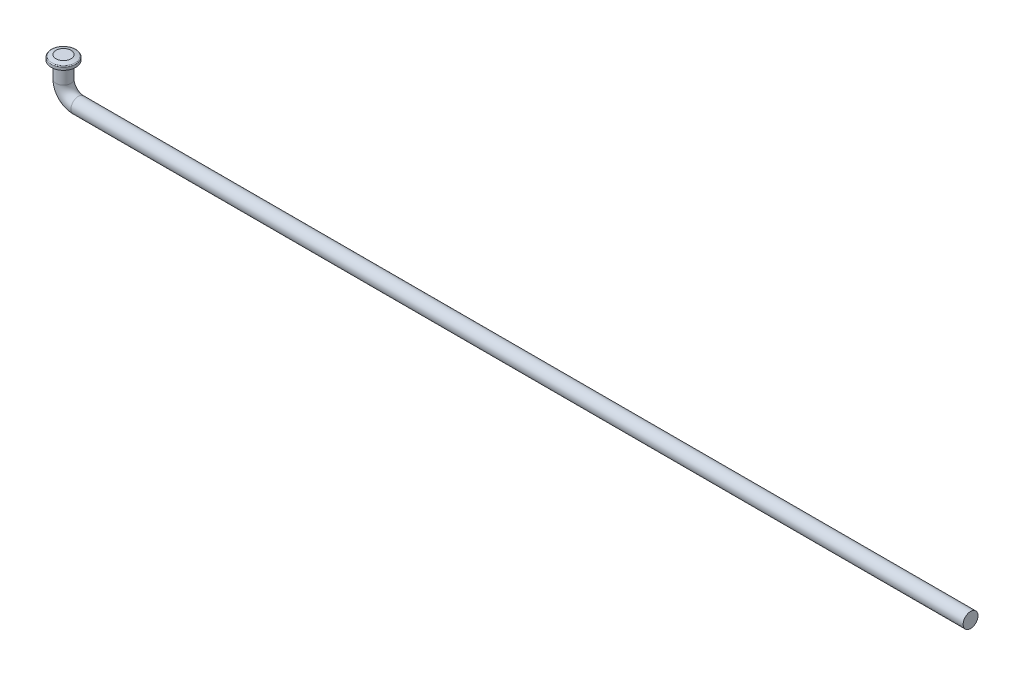
SolidWorks part; units mm, degrees
ref_plane "Спереди" through (0, 0, 0) normal (0, 0, 1) x (1, 0, 0)
ref_plane "Сверху" through (0, 0, 0) normal (0, 1, 0) x (1, 0, 0)
ref_plane "Справа" through (0, 0, 0) normal (1, 0, 0) x (0, 0, -1)
sketch "Эскиз1" plane through (0, 0, 0) normal (0, 0, 1) x (1, 0, 0)
  line L0 (-90, 0) -> (90, 0)
  line L1 (-93, 3) -> (-93, 6)
  arc A0 (-90, 0) -> (-93, 3) centre (-90, 3) cw
  point P4 (0, 0)
  dimension "D1" = 3
  dimension "D2" = 6
  dimension "D3" = 180
other "Round D3MM(1)"
ref_plane "Плоскость2" through (-90, 0, 0) normal (1, 0, 0) x (0, 1, 0)
sketch "Эскиз12" plane through (-90, 0, 0) normal (1, 0, 0) x (0, 1, 0)
  circle A0 centre (0, 0) radius 1.5
  point P3 (0, 0)
sketch "Эскиз13" plane through (0, 6, 0) normal (0, 1, 0) x (1, 0, 0)
  circle A0 centre (-93, 0) radius 2.5
extrude "Бобышка-Вытянуть1" add sketch "Эскиз13" along normal blind 1.3 separate body
chamfer "Фаска1" distance 0.3 distance2 1 1 edges at (-95.5, 7.3, 0)
chamfer "Фаска2" distance 0.3 angle 69 1 edges at (-95.5, 6, 0)
fillet "Скругление5" radius 0.2 1 edges at (-93, 7, 2.5)
sketch "Эскиз14" plane through (0, 0, 0) normal (0, 0, 1) x (1, 0, 0)
  line L0 (-84.5, 6) -> (-101.5, 6)
  point P4 (-93, 6)
